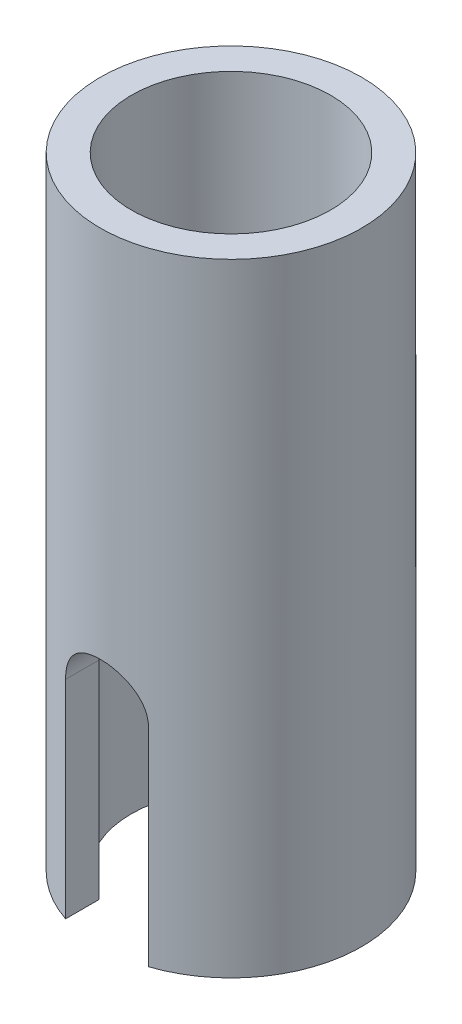
SolidWorks part; units mm, degrees
material "ABS"
ref_plane "Plan de face" through (0, 0, 0) normal (0, 0, 1) x (1, 0, 0)
ref_plane "Plan de dessus" through (0, 0, 0) normal (0, 1, 0) x (1, 0, 0)
ref_plane "Plan de droite" through (0, 0, 0) normal (1, 0, 0) x (0, 0, -1)
sketch "Esquisse1" plane through (0, 0, 0) normal (0, 0, 1) x (1, 0, 0)
  line L0 (0, 0) -> (4.8, 0) construction
  line L1 (4.8, 0) -> (6.3, 0)
  line L2 (6.3, 0) -> (6.3, 30)
  line L3 (6.3, 30) -> (4.8, 30)
  line L4 (4.8, 30) -> (4.8, 0)
  line L5 (0, 0) -> (0, 8.3326) construction
  dimension "D1" = 4.8
  dimension "D2" = 30
  dimension "D3" = 1.5
revolve "Révolution1" add sketch "Esquisse1" angle 360 about L5
sketch "Esquisse2" plane through (0, 0, 0) normal (0, 0, 1) x (1, 0, 0)
  line L0 (0, -10) -> (0, 10) construction
  line L1 (-2, -10) -> (-2, 10)
  line L2 (2, -10) -> (2, 10)
  arc A0 (-2, -10) -> (2, -10) centre (0, -10) ccw
  arc A1 (2, 10) -> (-2, 10) centre (0, 10) ccw
  point P2 (0, 0)
  dimension "D2" = 2
  dimension "D1" = 10
extrude "Enlèv. mat.-Extru.1" cut sketch "Esquisse2" against normal through all and the other way through all
